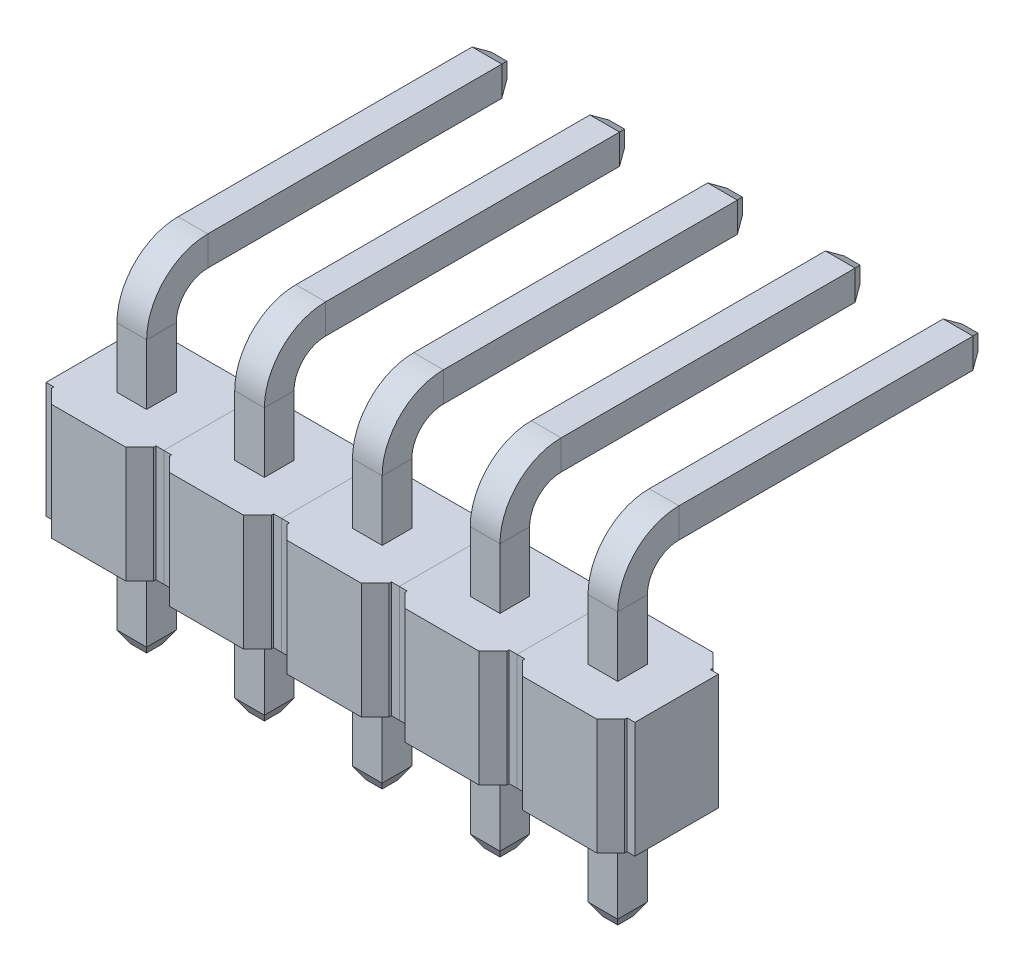
SolidWorks part; units mm, degrees
ref_plane "Front" through (0, 0, 0) normal (0, 0, 1) x (1, 0, 0)
ref_plane "Top" through (0, 0, 0) normal (0, 1, 0) x (1, 0, 0)
ref_plane "Right" through (0, 0, 0) normal (1, 0, 0) x (0, 0, -1)
sketch "Эскиз2" plane through (0, 0, 0) normal (1, 0, 0) x (0, 0, -1)
  line L0 (0, 0) -> (0, -2.2)
  line L1 (0, 0) -> (0, 3.8)
  line L2 (1, 4.8) -> (7.6, 4.8)
  arc A0 (1, 4.8) -> (0, 3.8) centre (1, 3.8) ccw
  point P7 (0, 4.8)
  dimension "D4" = 1
  dimension "D1" = 2.2
  dimension "D2" = 4.8
  dimension "D3" = 7.6
sketch "Эскиз3" plane through (0, 0, 0) normal (0, 1, 0) x (1, 0, 0)
  line L1 (-0.32, -0.32) -> (0.32, -0.32)
  line L2 (-0.32, -0.32) -> (-0.32, 0.32)
  line L3 (-0.32, 0.32) -> (0.32, 0.32)
  line L4 (0.32, -0.32) -> (0.32, 0.32)
  line L5 (-0.32, -0.32) -> (0.32, 0.32) construction
  line L6 (-0.32, 0.32) -> (0.32, -0.32) construction
  point P0 (0, 0)
sweep "По траектории1" add profiles "Эскиз3" path "Эскиз2"
chamfer "Фаска1" distance 0.15 angle 60 8 edges at (0, -2.2, -0.32) (-0.32, -2.2, 0) (0, -2.2, 0.32) (0.32, -2.2, 0) (0, 5.12, -7.6) (-0.32, 4.8, -7.6) (0, 4.48, -7.6) (0.32, 4.8, -7.6)
sketch "Эскиз4" plane through (0, 0, 0) normal (0, 1, 0) x (1, 0, 0)
  line L0 (-1.1, 0.9) -> (-1.1, 1.25)
  line L1 (-1.1, -1.25) -> (1.1, -1.25)
  line L2 (-1.1, -1.25) -> (-1.1, -0.9)
  line L3 (-1.1, 1.25) -> (1.1, 1.25)
  line L4 (1.1, -1.25) -> (1.1, -0.9)
  line L5 (-1.1, -1.25) -> (1.1, 1.25) construction
  line L6 (-1.1, 1.25) -> (1.1, -1.25) construction
  line L7 (-1.27, -0.9) -> (-1.1, -0.9)
  line L8 (-1.27, -0.9) -> (-1.27, 0.9)
  line L9 (-1.27, 0.9) -> (-1.1, 0.9)
  line L10 (1.27, -0.9) -> (1.27, 0.9)
  line L11 (-1.27, -0.9) -> (1.27, 0.9) construction
  line L12 (-1.27, 0.9) -> (1.27, -0.9) construction
  line L13 (1.1, 0.9) -> (1.1, 1.25)
  line L14 (1.1, -0.9) -> (1.27, -0.9)
  line L15 (1.1, 0.9) -> (1.27, 0.9)
  point P0 (0, 0)
  point P5 (0, 0)
  dimension "D1" = 2.2
  dimension "D2" = 2.5
  dimension "D3" = 1.8
  dimension "D4" = 2.54
extrude "Бобышка-Вытянуть1" add sketch "Эскиз4" along normal blind 2.5 separate body
chamfer "Фаска2" distance 0.3 angle 45 4 edges at (-1.1, 1.25, -1.25) (1.1, 1.25, -1.25) (-1.1, 1.25, 1.25) (1.1, 1.25, 1.25)
pattern_linear "Линейный массив1" count 5 spacing 2.54 along (-1, 0, 0) of bodies 102 101
